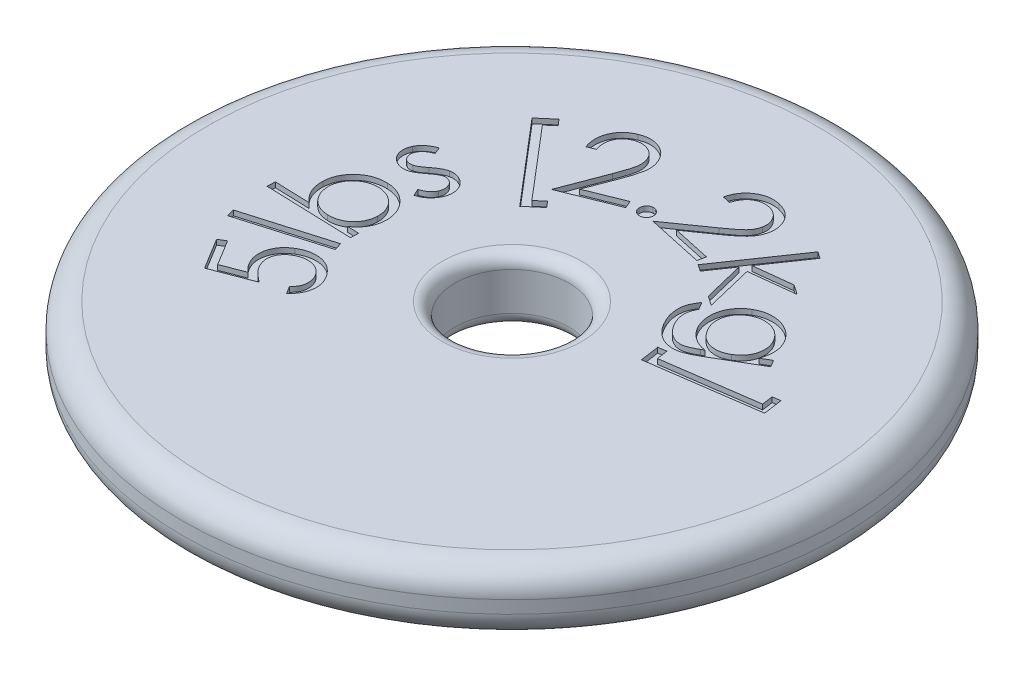
SolidWorks part; units mm, degrees
ref_plane "Front Plane" through (0, 0, 0) normal (0, 0, 1) x (1, 0, 0)
ref_plane "Top Plane" through (0, 0, 0) normal (0, 1, 0) x (1, 0, 0)
ref_plane "Right Plane" through (0, 0, 0) normal (1, 0, 0) x (0, 0, -1)
sketch "Sketch1" plane through (0, 0, 0) normal (0, 1, 0) x (1, 0, 0)
  circle A0 centre (0, 0) radius 82.55
  circle A1 centre (0, 0) radius 14.2875
  dimension "D1" = 165.1
extrude "Boss-Extrude1" add sketch "Sketch1" along normal mid plane 15.875
fillet "Fillet1" radius 6.35 2 edges at (0, -7.9375, 82.55) (0, 7.9375, 82.55)
fillet "Fillet2" radius 3.175 2 edges at (0, -7.9375, 14.2875) (0, 7.9375, 14.2875)
sketch "Sketch2" plane through (0, 7.9375, 0) normal (0, 1, 0) x (1, 0, 0)
  circle A0 centre (0, 0) radius 35.2348 construction
  text T0 "5lbs [2.2kg]" font "Century Gothic" height in points 80
extrude "Cut-Extrude1" cut sketch "Sketch2" against normal blind 1.27
